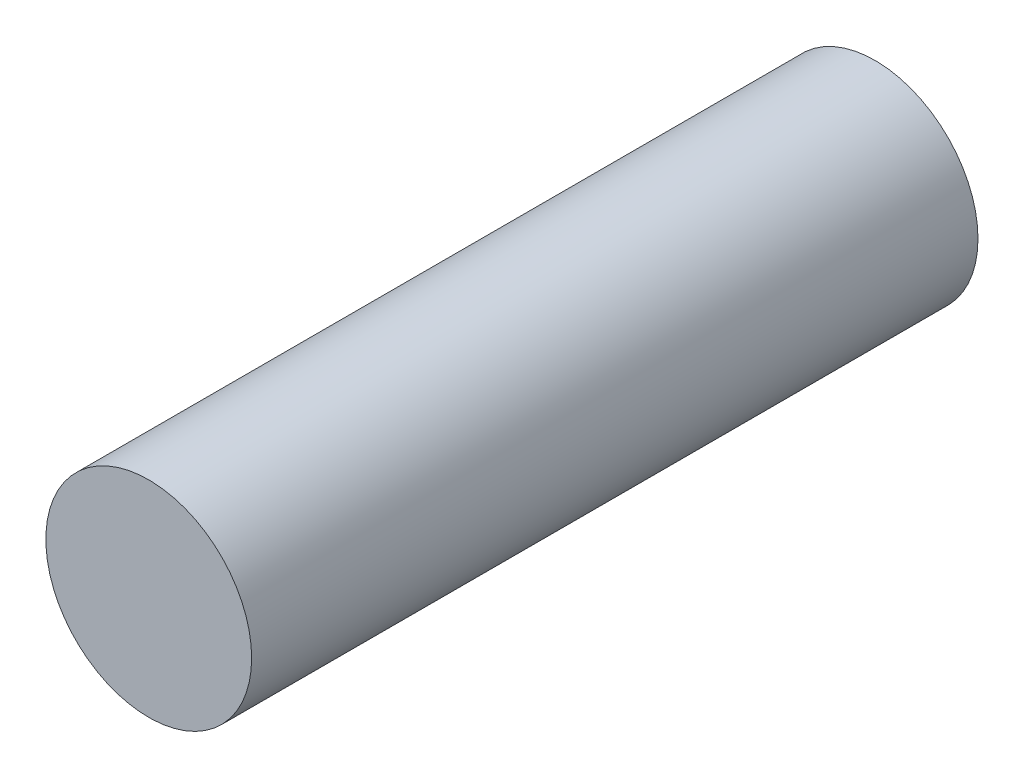
SolidWorks part; units mm, degrees
ref_plane "Front Plane" through (0, 0, 0) normal (0, 0, 1) x (1, 0, 0)
ref_plane "Top Plane" through (0, 0, 0) normal (0, 1, 0) x (1, 0, 0)
ref_plane "Right Plane" through (0, 0, 0) normal (1, 0, 0) x (0, 0, -1)
sketch "Sketch1" plane through (0, 0, 0) normal (0, 0, 1) x (1, 0, 0)
  circle A0 centre (0, 0) radius 42.5
  dimension "D1" = 85
extrude "Boss-Extrude1" add sketch "Sketch1" along normal blind 300 contours A0
